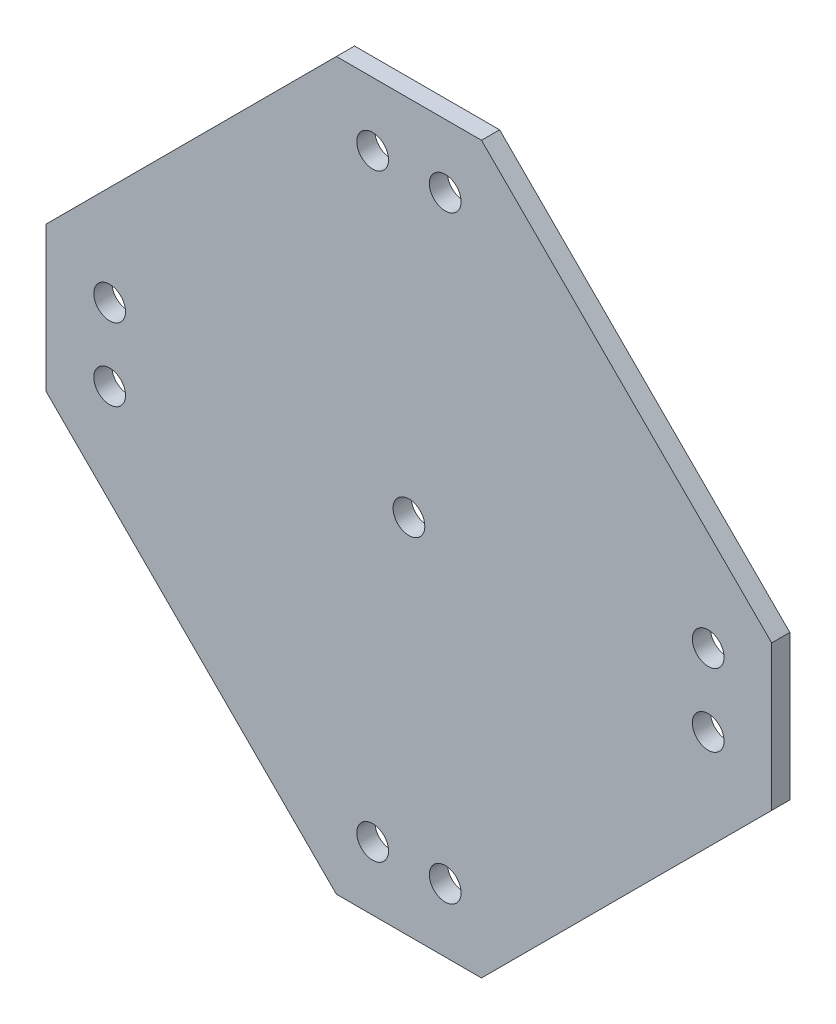
SolidWorks part; units mm, degrees
ref_plane "Front Plane" through (0, 0, 0) normal (0, 0, 1) x (1, 0, 0)
ref_plane "Top Plane" through (0, 0, 0) normal (0, 1, 0) x (1, 0, 0)
ref_plane "Right Plane" through (0, 0, 0) normal (1, 0, 0) x (0, 0, -1)
sketch "Sketch1" plane through (0, 0, 0) normal (0, 0, 1) x (1, 0, 0)
  line L0 (-8, 40) -> (8, 40)
  line L1 (8, 40) -> (40, 8)
  line L2 (40, 8) -> (40, -8)
  line L3 (40, -8) -> (8, -40)
  line L4 (8, -40) -> (-8, -40)
  line L5 (-8, -40) -> (-40, -8)
  line L6 (-40, -8) -> (-40, 8)
  line L7 (-40, 8) -> (-8, 40)
  line L8 (-40, 0) -> (40, 0) construction
  line L9 (0, 40) -> (0, -40) construction
  line L10 (-8, 40) -> (-8, -40) construction
  line L11 (8, 40) -> (8, -40) construction
  line L12 (40, -8) -> (-40, -8) construction
  line L13 (-40, 8) -> (40, 8) construction
  point P12 (0, 0)
  point P13 (0, 0)
  dimension "D1" = 16
  dimension "D2" = 80
  dimension "D3" = 80
  dimension "D4" = 16
extrude "Boss-Extrude1" add sketch "Sketch1" along normal blind 2
sketch "Sketch2" plane through (0, 0, 2) normal (0, 0, 1) x (1, 0, 0)
  line L0 (-4, 33) -> (4, 33) construction
  line L1 (0, 33) -> (0, 40) construction
  line L2 (8, 40) -> (-8, 40) construction
  circle A0 centre (-4, 33) radius 1.75
  circle A1 centre (4, 33) radius 1.75
  circle A2 centre (0, 0) radius 1.75
  dimension "D3" = 3.5
  dimension "D4" = 3.5
  dimension "D5" = 3.5
  dimension "D1" = 7
  dimension "D2" = 8
extrude "Cut-Extrude1" cut sketch "Sketch2" against normal through all both
pattern_circular "CirPattern1" count 4 every 90 about axis through (0, 0, 0) along (0, 0, 1) of "Cut-Extrude1"
